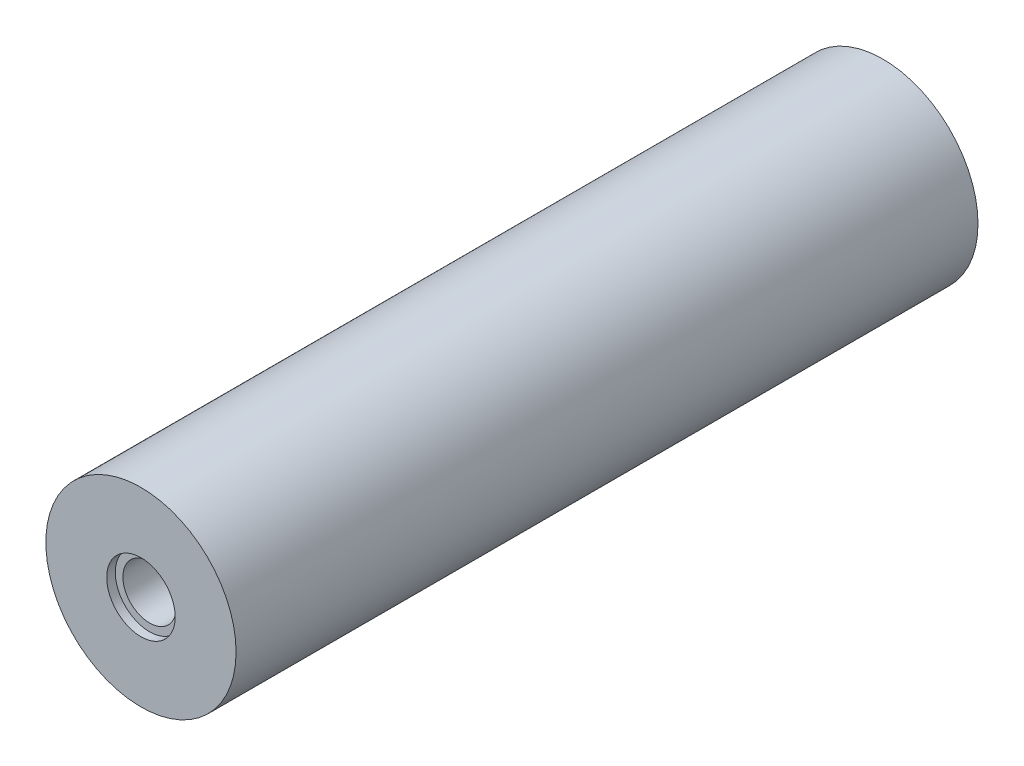
SolidWorks part; units mm, degrees
material "Petg 30% Infill"
ref_plane "Front Plane" through (0, 0, 0) normal (0, 0, 1) x (1, 0, 0)
ref_plane "Top Plane" through (0, 0, 0) normal (0, 1, 0) x (1, 0, 0)
ref_plane "Right Plane" through (0, 0, 0) normal (1, 0, 0) x (0, 0, -1)
sketch "Sketch1" plane through (0, 0, 0) normal (0, 0, 1) x (1, 0, 0)
  circle A0 centre (0, 0) radius 10
  dimension "D1" = 20
extrude "Boss-Extrude1" add sketch "Sketch1" along normal blind 78
sketch "Sketch2" plane through (0, 0, 78) normal (0, 0, 1) x (1, 0, 0)
  circle A0 centre (0, 0) radius 2.8
  dimension "D1" = 5.6
extrude "Cut-Extrude1" cut sketch "Sketch2" against normal blind 20
ref_plane "Plane1" through (0, 0, 39) normal (0, 0, 1) x (1, 0, 0)
sketch "Sketch3" plane through (0, 0, 78) normal (0, 0, 1) x (1, 0, 0)
  circle A0 centre (0, 0) radius 3.6
  circle A1 centre (0, 0) radius 10 construction
  point P4 (0, 0)
  dimension "D1" = 7.2
extrude "Cut-Extrude2" cut sketch "Sketch3" against normal blind 0.9
sketch "Sketch4" plane through (0, 0, 0) normal (0, 0, -1) x (-1, 0, 0)
  circle A0 centre (0, 0) radius 1.8
  dimension "D1" = 3.6
extrude "Cut-Extrude3" cut sketch "Sketch4" against normal blind 20
chamfer "Chamfer2" distance 2 angle 10 1 edges at (-1.8, 0, 0)
